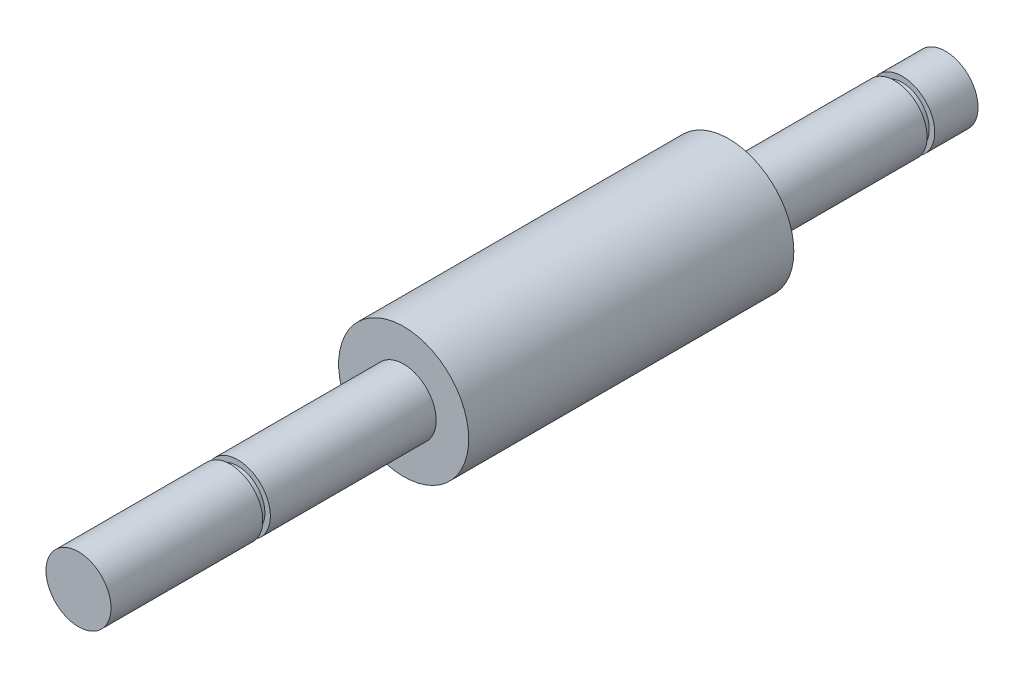
SolidWorks part; units mm, degrees
ref_plane "前视基准面" through (0, 0, 0) normal (0, 0, 1) x (1, 0, 0)
ref_plane "上视基准面" through (0, 0, 0) normal (0, 1, 0) x (1, 0, 0)
ref_plane "右视基准面" through (0, 0, 0) normal (1, 0, 0) x (0, 0, -1)
sketch "草图1" plane through (0, 0, 0) normal (0, 0, 1) x (1, 0, 0)
  circle A0 centre (0, 0) radius 6
  dimension "D1" = 12
extrude "凸台-拉伸1" add sketch "草图1" along normal blind 30
sketch "草图2" plane through (0, 0, 0) normal (0, 0, -1) x (-1, 0, 0)
  circle A0 centre (0, 0) radius 3
  dimension "D1" = 6
extrude "凸台-拉伸2" add sketch "草图2" along normal blind 20
sketch "草图3" plane through (0, 0, 30) normal (0, 0, 1) x (1, 0, 0)
  circle A0 centre (0, 0) radius 3
  dimension "D1" = 6
extrude "凸台-拉伸3" add sketch "草图3" along normal blind 30
ref_plane "基准面1" through (0, 0, -16) normal (0, 0, -1) x (-1, 0, 0)
sketch "草图4" plane through (0, 0, -16) normal (0, 0, -1) x (-1, 0, 0)
  circle A0 centre (0, 0) radius 6.7074
  circle A1 centre (0, 0) radius 2.5
  dimension "D1" = 5
extrude "切除-拉伸1" cut sketch "草图4" against normal blind 0.7
ref_plane "基准面2" through (0, 0, 45.3) normal (0, 0, -1) x (-1, 0, 0)
sketch "草图5" plane through (0, 0, 45.3) normal (0, 0, -1) x (-1, 0, 0)
  circle A0 centre (0, 0) radius 8.2911
  circle A1 centre (0, 0) radius 2.5
  dimension "D1" = 5
extrude "切除-拉伸2" cut sketch "草图5" against normal blind 0.7
